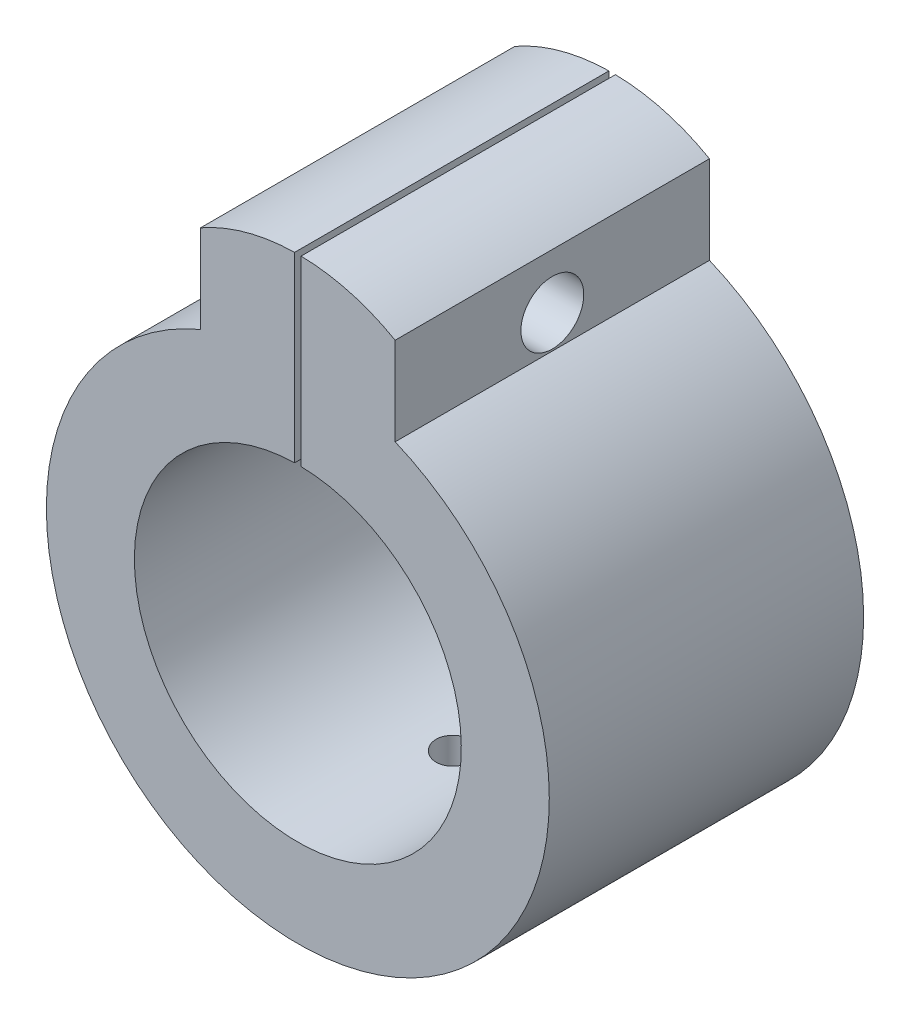
SolidWorks part; units mm, degrees
material "6061 合金"
ref_plane "前视基准面" through (0, 0, 0) normal (0, 0, 1) x (1, 0, 0)
ref_plane "上视基准面" through (0, 0, 0) normal (0, 1, 0) x (1, 0, 0)
ref_plane "右视基准面" through (0, 0, 0) normal (1, 0, 0) x (0, 0, -1)
sketch "草图1" plane through (0, 0, 0) normal (0, 0, 1) x (1, 0, 0)
  line L0 (-7.7403, 18.4415) -> (-7.7403, 25.4415)
  line L1 (-35, -7) -> (-35, 7)
  line L2 (-35, 7) -> (-7.7403, 18.4415)
  line L3 (-35, -7) -> (-7.7403, -18.4415)
  line L4 (7.7403, 18.4415) -> (7.7403, 25.4415)
  line L5 (35, -7) -> (7.7403, -18.4415)
  line L6 (35, -7) -> (35, 7)
  line L7 (35, 7) -> (7.7403, 18.4415)
  line L8 (0, 0) -> (-28, 0) construction
  circle A0 centre (0, 0) radius 13
  arc A1 (-7.7403, 18.4415) -> (7.7403, 18.4415) centre (0, 0) ccw
  arc A2 (-7.7403, 25.4415) -> (7.7403, 25.4415) centre (0, 11.8749) cw
  circle A3 centre (-28, 0) radius 3.5
  circle A4 centre (28, 0) radius 3.5
  dimension "D1" = 28
  dimension "D3" = 26
  dimension "D4" = 20
  dimension "D5" = 7
  dimension "D6" = 7
  dimension "D2" = 28
  dimension "D7" = 70
extrude "凸台-拉伸2" add sketch "草图1" along normal blind 10 contours A1 L5 L6 L7 | A2 L0 A1 L4 A0 | A1 L2 L1 L3
sketch "草图2" plane through (0, 0, 10) normal (0, 0, 1) x (1, 0, 0)
  line L0 (-7.7403, 18.4415) -> (-7.7403, 25.4415)
  line L1 (7.7403, 18.4415) -> (7.7403, 25.4415)
  circle A0 centre (0, 0) radius 13
  arc A1 (-7.7403, 18.4415) -> (7.7403, 18.4415) centre (0, 0) ccw
  arc A2 (-7.7403, 25.4415) -> (7.7403, 25.4415) centre (0, 11.8749) cw
extrude "凸台-拉伸3" add sketch "草图2" along normal blind 15
sketch "草图3" plane through (0, 0, 25) normal (0, 0, 1) x (1, 0, 0)
  line L1 (-0.2586, 12.3781) -> (-0.2586, 31.1043)
  line L2 (0.2586, 12.3781) -> (0.2586, 31.1043)
  line L3 (-0.2586, 12.3781) -> (0.2586, 12.3781)
  line L4 (-0.2586, 31.1043) -> (0.2586, 31.1043)
extrude "切除-拉伸1" cut sketch "草图3" against normal through all
sketch "草图4" plane through (7.7403, 0, 0) normal (1, 0, 0) x (0, 0, -1)
  circle A0 centre (-12.5, 21.0864) radius 2.5
extrude "切除-拉伸2" cut sketch "草图4" against normal through all
sketch "草图5" plane through (0, 0, 10) normal (0, 0, 1) x (1, 0, 0)
  line L0 (-7.7403, 18.4415) -> (-35, 7)
  line L1 (-35, 7) -> (-35, -7)
  line L2 (-35, -7) -> (-7.7403, -18.4415)
  line L3 (7.7403, 18.4415) -> (35, 7)
  line L4 (35, 7) -> (35, -7)
  line L5 (35, -7) -> (7.7403, -18.4415)
  arc A0 (-7.7403, 18.4415) -> (-7.7403, -18.4415) centre (0, 0) ccw
  arc A1 (7.7403, -18.4415) -> (7.7403, 18.4415) centre (0, 0) ccw
extrude "切除-拉伸3" cut sketch "草图5" against normal through all
sketch "草图6" plane through (0, 0, 0) normal (0, 1, 0) x (1, 0, 0)
  line L0 (0, 0) -> (0, -25) construction
  line L1 (-20, -25) -> (20, -25) construction
  circle A0 centre (0, -12.5) radius 1.5
  dimension "D1" = 3
extrude "切除-拉伸4" cut sketch "草图6" against normal through all contours A0
